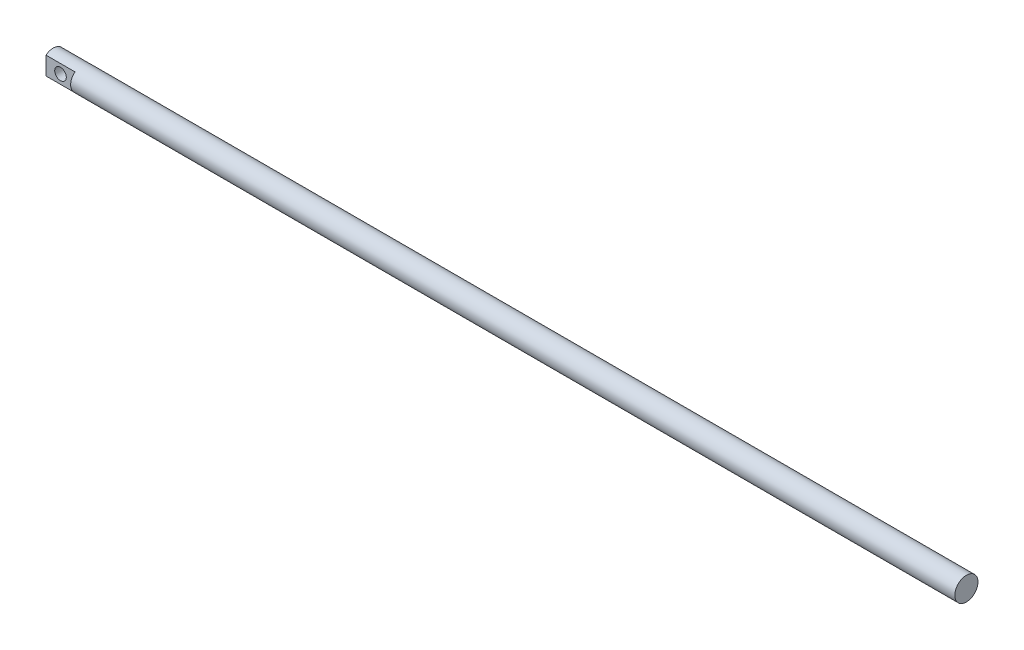
SolidWorks part; units mm, degrees
ref_plane "前视基准面" through (0, 0, 0) normal (0, 0, 1) x (1, 0, 0)
ref_plane "上视基准面" through (0, 0, 0) normal (0, 1, 0) x (1, 0, 0)
ref_plane "右视基准面" through (0, 0, 0) normal (1, 0, 0) x (0, 0, -1)
sketch "草图1" plane through (0, 0, 0) normal (1, 0, 0) x (0, 0, -1)
  circle A0 centre (0, 0) radius 8
  dimension "D1" = 16
extrude "凸台-拉伸1" add sketch "草图1" along normal blind 630
sketch "草图3" plane through (0, 0, 0) normal (-1, 0, 0) x (0, 0, 1)
  line L1 (-5, 10) -> (5, 10)
  line L2 (-5, 10) -> (-5, -10)
  line L3 (-5, -10) -> (5, -10)
  line L4 (5, 10) -> (5, -10)
  line L5 (-5, 10) -> (5, -10) construction
  line L6 (-5, -10) -> (5, 10) construction
  point P0 (0, 0)
  dimension "D1" = 20
  dimension "D2" = 10
extrude "切除-拉伸1" cut sketch "草图3" against normal blind 20 flip side to cut
sketch "草图4" plane through (0, 0, -5) normal (0, 0, -1) x (-1, 0, 0)
  line L0 (0, 6.245) -> (-20, 6.245) construction
  circle A0 centre (-10, 0) radius 4
  point P6 (-10, 6.245)
  dimension "D1" = 8
extrude "切除-拉伸3" cut sketch "草图4" against normal blind 20
